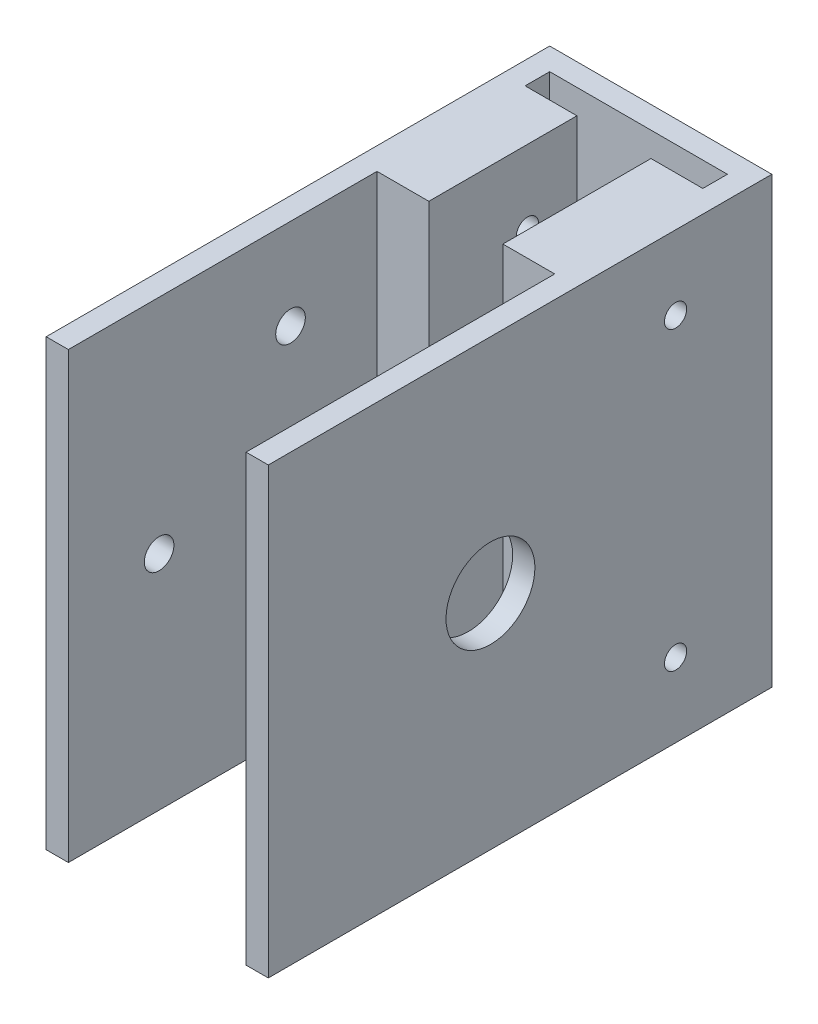
SolidWorks part; units mm, degrees
ref_plane "Front Plane" through (0, 0, 0) normal (0, 0, 1) x (1, 0, 0)
ref_plane "Top Plane" through (0, 0, 0) normal (0, 1, 0) x (1, 0, 0)
ref_plane "Right Plane" through (0, 0, 0) normal (1, 0, 0) x (0, 0, -1)
sketch "Sketch1" plane through (0, 0, 0) normal (0, 0, 1) x (1, 0, 0)
  line L0 (55, 0) -> (-55, 0) construction
  line L1 (-15, 30) -> (15, 30)
  line L2 (-15, 30) -> (-15, -30)
  line L3 (-15, -30) -> (15, -30)
  line L4 (15, 30) -> (15, -30)
  line L5 (-15, 30) -> (15, -30) construction
  line L6 (-15, -30) -> (15, 30) construction
  circle A0 centre (0, 15) radius 2.9
  circle A1 centre (0, -15) radius 2.9
  point P0 (0, 0)
  dimension "D3" = 15
  dimension "D4" = 5.8
  dimension "D1" = 30
  dimension "D2" = 60
extrude "Boss-Extrude1" add sketch "Sketch1" along normal blind 3
sketch "Sketch2" plane through (0, 0, 3) normal (0, 0, 1) x (1, 0, 0)
  line L0 (-15, -30) -> (15, -30) construction
  line L1 (-15, 30) -> (-12, 30)
  line L2 (-15, 30) -> (-15, -30)
  line L3 (-15, -30) -> (-12, -30)
  line L4 (-12, 30) -> (-12, -30)
  line L6 (15, 30) -> (12, 30)
  line L7 (15, 30) -> (15, -30)
  line L8 (15, -30) -> (12, -30)
  line L9 (12, 30) -> (12, -30)
  dimension "D1" = 3
  dimension "D2" = 3
extrude "Boss-Extrude2" add sketch "Sketch2" along normal blind 65
sketch "Sketch5" plane through (0, 30, 0) normal (0, 1, 0) x (1, 0, 0)
  line L0 (12, -68) -> (12, -3) construction
  line L2 (12, -6.3201) -> (5, -6.3201)
  line L3 (12, -6.3201) -> (12, -26.3201)
  line L4 (12, -26.3201) -> (5, -26.3201)
  line L5 (5, -6.3201) -> (5, -26.3201)
  line L6 (0, -33) -> (0, 33) construction
  line L7 (-12, -26.3201) -> (-5, -26.3201)
  line L8 (-12, -6.3201) -> (-5, -6.3201)
  line L9 (-5, -6.3201) -> (-5, -26.3201)
  line M5 (-12, -68) -> (-12, -3)
  line M7 (12, -3) -> (12, -68)
  dimension "D1" = 7
  dimension "D2" = 20
extrude "Boss-Extrude3" add sketch "Sketch5" against normal up to surface (60 mm away) contours L2 L5 L4 M7 | L9 L8 L7 M5 up to face at (0, -30, 34.75)
sketch "Sketch3" plane through (-15, 0, 0) normal (-1, 0, 0) x (0, 0, 1)
  line L0 (68, 30) -> (0, 30) construction
  line L1 (0, 30) -> (0, -30) construction
  line L3 (16.5, 0) -> (-16.5, 0) construction
  circle A0 centre (13, 20) radius 1.5
  circle A1 centre (38, 0) radius 6
  circle A2 centre (20.25, 0) radius 2
  circle A4 centre (38, 17.75) radius 2
  circle A5 centre (55.75, 0) radius 2
  circle A6 centre (38, -17.75) radius 2
  circle A7 centre (13, -20) radius 1.5
  point P20 (38, 0)
  dimension "D1" = 3
  dimension "D2" = 10
  dimension "D3" = 13
  dimension "D4" = 12
  dimension "D5" = 4
  dimension "D6" = 17.75
  dimension "D7" = 38
extrude "Cut-Extrude1" cut sketch "Sketch3" against normal up to next
sketch "Sketch4" plane through (12, 0, 0) normal (-1, 0, 0) x (0, 0, 1)
  circle A0 centre (13, -20) radius 1.5 construction
  circle A1 centre (13, 20) radius 1.5 construction
  circle A2 centre (38, 0) radius 6 construction
  circle A3 centre (13, -20) radius 1.5
  circle A4 centre (13, 20) radius 1.5
  circle A5 centre (38, 0) radius 6
extrude "Cut-Extrude2" cut sketch "Sketch4" against normal through all both and the other way through all
